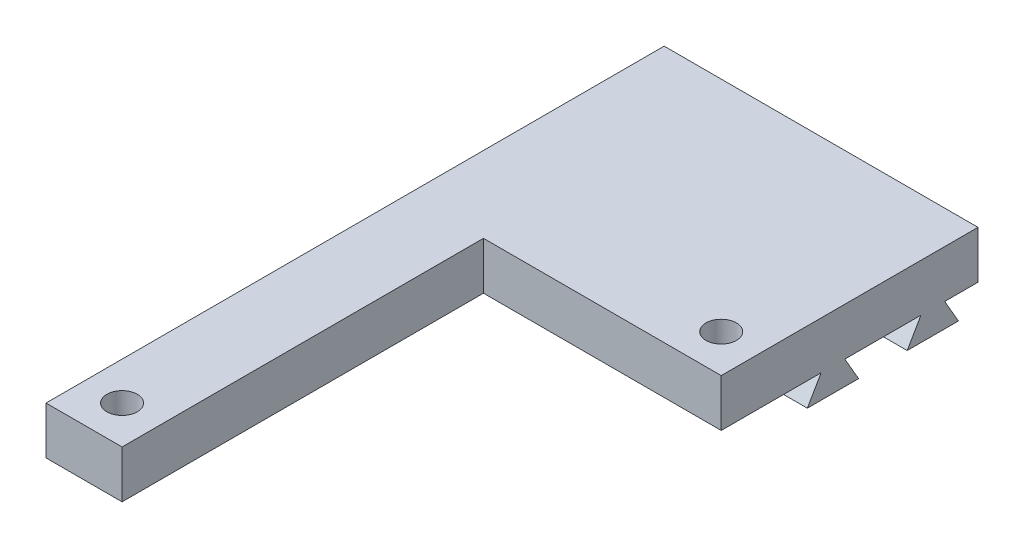
SolidWorks part; units mm, degrees
ref_plane "Front Plane" through (0, 0, 0) normal (0, 0, 1) x (1, 0, 0)
ref_plane "Top Plane" through (0, 0, 0) normal (0, 1, 0) x (1, 0, 0)
ref_plane "Right Plane" through (0, 0, 0) normal (1, 0, 0) x (0, 0, -1)
sketch "Sketch1" plane through (0, 0, 0) normal (0, 1, 0) x (1, 0, 0)
  line L0 (16.5, 10) -> (-8.5, 10)
  line L1 (-16.5, -30) -> (-8.5, -30)
  line L2 (-16.5, -30) -> (-16.5, 30)
  line L3 (-16.5, 30) -> (16.5, 30)
  line L4 (16.5, 10) -> (16.5, 30)
  line L7 (-8.5, 10) -> (-8.5, -30)
  line L8 (-8.5, -30) -> (-16.5, -30)
  line L9 (16.5, 30) -> (16.5, 10)
  line L10 (16.5, 30) -> (16.5, 10)
  point P0 (0, 0)
  dimension "D1" = 33
  dimension "D3" = 25
  dimension "D4" = 20
extrude "Boss-Extrude1" add sketch "Sketch1" along normal blind 5 contours L7 L0 L4 L3 L2 L1
sketch "Sketch3" plane through (16.5, 0, 0) normal (1, 0, 0) x (0, 0, -1)
  line L0 (24, 0) -> (22.5566, -2.5)
  line L1 (10, 0) -> (30, 0) construction
  line L2 (22.5566, -2.5) -> (27.9434, -2.5)
  line L3 (27.9434, -2.5) -> (26.5, 0)
  line L4 (26.5, 0) -> (24, 0)
  line L5 (20, 4.7114) -> (20, -4.7114)
  line L6 (12.0566, -2.5) -> (13.5, 0)
  line L7 (17.4434, -2.5) -> (12.0566, -2.5)
  line L8 (16, 0) -> (17.4434, -2.5)
  line L9 (13.5, 0) -> (16, 0)
  point P9 (20, 0)
  line M6 (10, 0) -> (30, 0)
  dimension "D1" = 2.5
  dimension "D2" = 3.5
  dimension "D3" = 60
  dimension "D4" = 60
  dimension "D5" = 2.5
  dimension "D6" = 5.3868
extrude "Boss-Extrude3" add sketch "Sketch3" against normal blind 33 contours L8 L6 L7 M6 | L2 L3 L4 L0
sketch "Sketch4" plane through (0, 0, -10) normal (0, 0, 1) x (1, 0, 0)
  line L1 (-8.5, 5) -> (16.5, 5)
  line L2 (-8.5, 5) -> (-8.5, 0)
  line L3 (-8.5, 0) -> (16.5, 0)
  line L4 (16.5, 5) -> (16.5, 0)
extrude "Boss-Extrude4" add sketch "Sketch4" along normal blind 7
sketch "Sketch5" plane through (0, 0, 30) normal (0, 0, 1) x (1, 0, 0)
  line L0 (-16.5, 0) -> (16.5, 0) construction
  line L1 (-16.5, 5) -> (-8.5, 5)
  line L2 (-16.5, 5) -> (-16.5, 0)
  line L3 (-16.5, 0) -> (-8.5, 0)
  line L4 (-8.5, 5) -> (-8.5, 0)
  line L5 (-16.5, 0) -> (-8.5, 0) construction
extrude "Boss-Extrude5" add sketch "Sketch5" along normal blind 5
sketch "Sketch6" plane through (0, 5, 0) normal (0, 1, 0) x (1, 0, 0)
  line L0 (16.5, 3) -> (16.5, 30) construction
  line L1 (16.5, 3) -> (-8.5, 3) construction
  line L2 (-8.5, -35) -> (-16.5, -35) construction
  line L3 (-16.5, -35) -> (-16.5, 30) construction
  circle A0 centre (12.5, 7) radius 1.6
  circle A1 centre (-12.5, -31) radius 1.6
  dimension "D1" = 3.2
  dimension "D2" = 3.2
  dimension "D3" = 4
  dimension "D4" = 4
  dimension "D5" = 4
  dimension "D6" = 4
extrude "Cut-Extrude1" cut sketch "Sketch6" against normal blind 5
